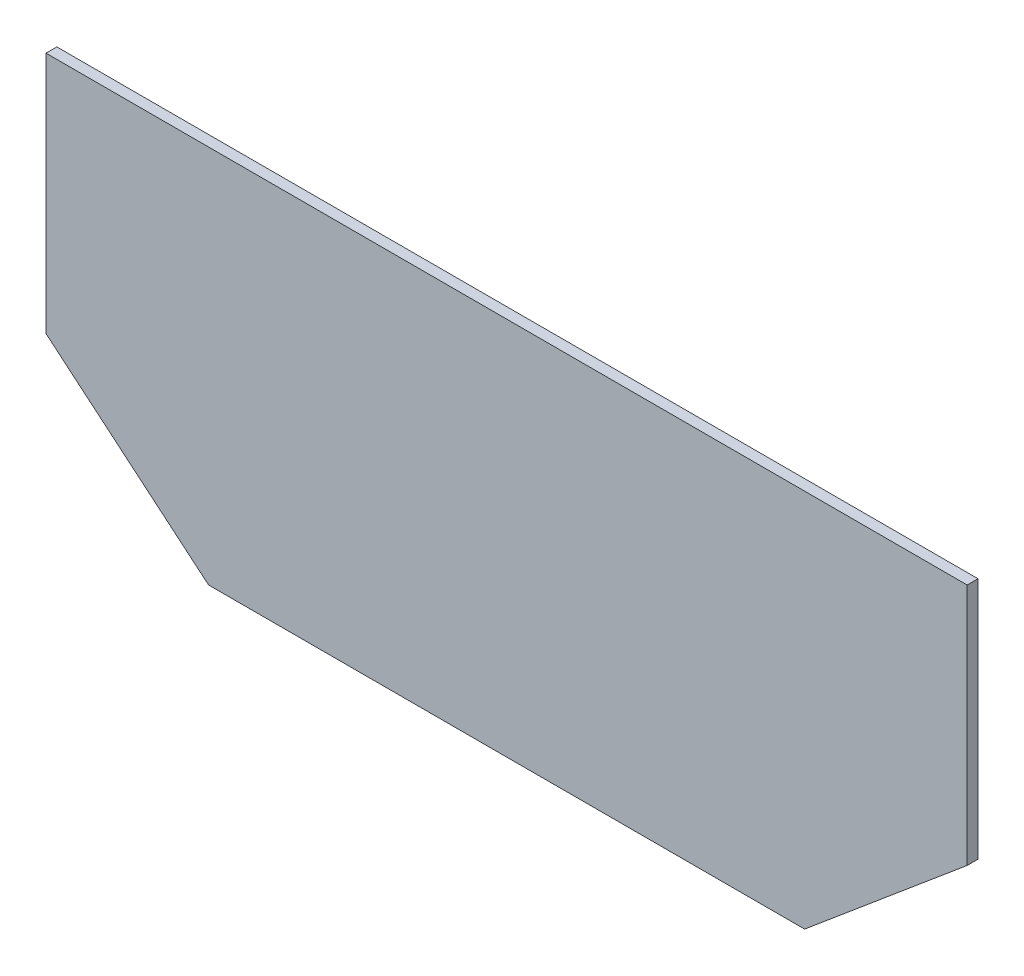
SolidWorks part; units mm, degrees
ref_plane "Plano frontal" through (0, 0, 0) normal (0, 0, 1) x (1, 0, 0)
ref_plane "Plano superior" through (0, 0, 0) normal (0, 1, 0) x (1, 0, 0)
ref_plane "Plano direito" through (0, 0, 0) normal (1, 0, 0) x (0, 0, -1)
sketch "Esboço1" plane through (0, 0, 0) normal (0, 0, 1) x (1, 0, 0)
  line L0 (0, -38.3153) -> (0, 142.1323) construction
  line L1 (55, 0) -> (-55, 0)
  line L2 (-55, 0) -> (-85, 25.173)
  line L3 (-85, 25.173) -> (-85, 70)
  line L4 (-85, 70) -> (85, 70)
  line L5 (85, 25.173) -> (85, 70)
  line L6 (55, 0) -> (85, 25.173)
  point P7 (0, 70)
  point P11 (0, 0)
  dimension "D1" = 85
  dimension "D2" = 40
  dimension "D3" = 70
  dimension "D4" = 110
extrude "Ressalto-extrusão1" add sketch "Esboço1" along normal blind 2
